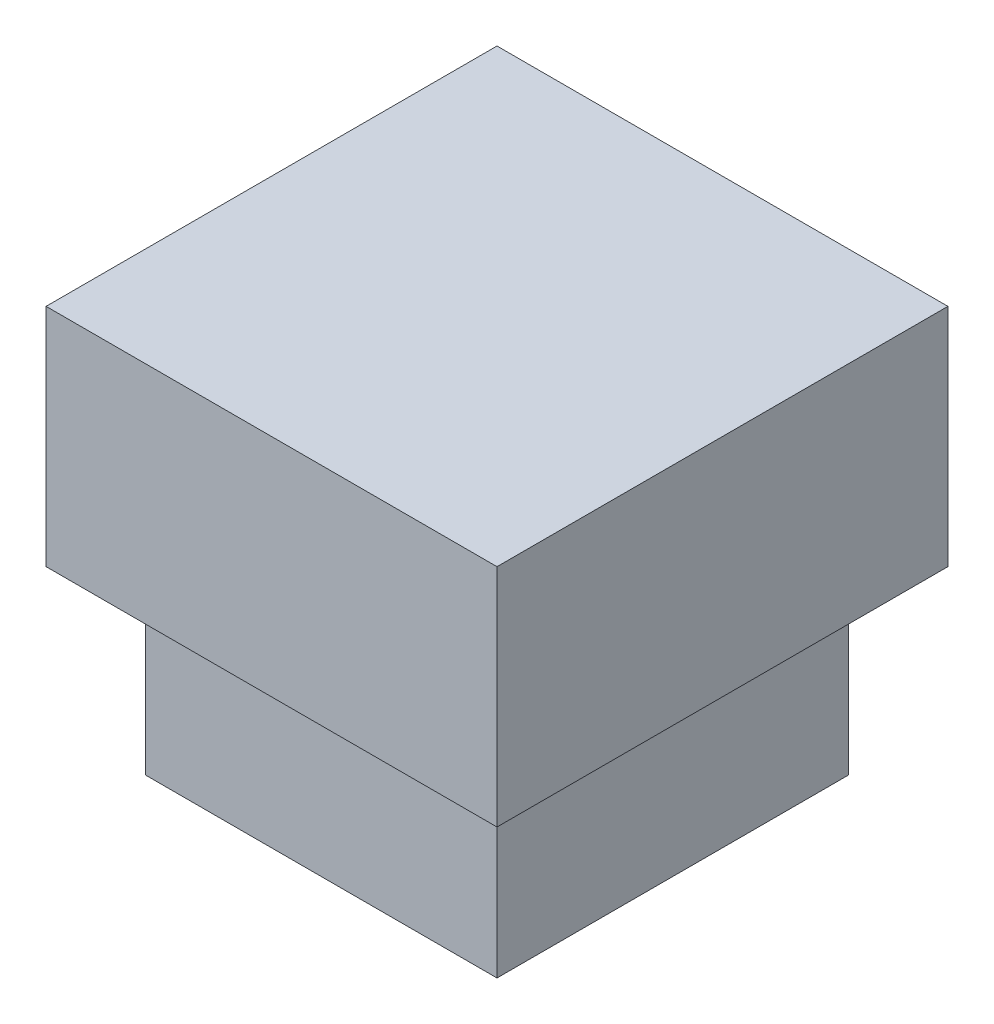
SolidWorks part; units mm, degrees
ref_plane "Спереди" through (0, 0, 0) normal (0, 0, 1) x (1, 0, 0)
ref_plane "Сверху" through (0, 0, 0) normal (0, 1, 0) x (1, 0, 0)
ref_plane "Справа" through (0, 0, 0) normal (1, 0, 0) x (0, 0, -1)
sketch "Эскиз1" plane through (0, 0, 0) normal (0, 1, 0) x (1, 0, 0)
  line L1 (-1.95, 1.95) -> (1.95, 1.95)
  line L2 (-1.95, 1.95) -> (-1.95, -1.95)
  line L3 (-1.95, -1.95) -> (1.95, -1.95)
  line L4 (1.95, 1.95) -> (1.95, -1.95)
  line L5 (-1.95, 1.95) -> (1.95, -1.95) construction
  line L6 (-1.95, -1.95) -> (1.95, 1.95) construction
  point P0 (0, 0)
  dimension "D1" = 3.9
  dimension "D2" = 3.9
extrude "Бобышка-Вытянуть1" add sketch "Эскиз1" along normal blind 2
sketch "Эскиз2" plane through (0, 2, 0) normal (0, 1, 0) x (1, 0, 0)
  line L1 (-2.5, 2.5) -> (2.5, 2.5)
  line L2 (-2.5, 2.5) -> (-2.5, -2.5)
  line L3 (-2.5, -2.5) -> (2.5, -2.5)
  line L4 (2.5, 2.5) -> (2.5, -2.5)
  line L5 (-2.5, 2.5) -> (2.5, -2.5) construction
  line L6 (-2.5, -2.5) -> (2.5, 2.5) construction
  point P0 (0, 0)
  dimension "D1" = 5
  dimension "D2" = 5
extrude "Бобышка-Вытянуть2" add sketch "Эскиз2" along normal blind 2.5
